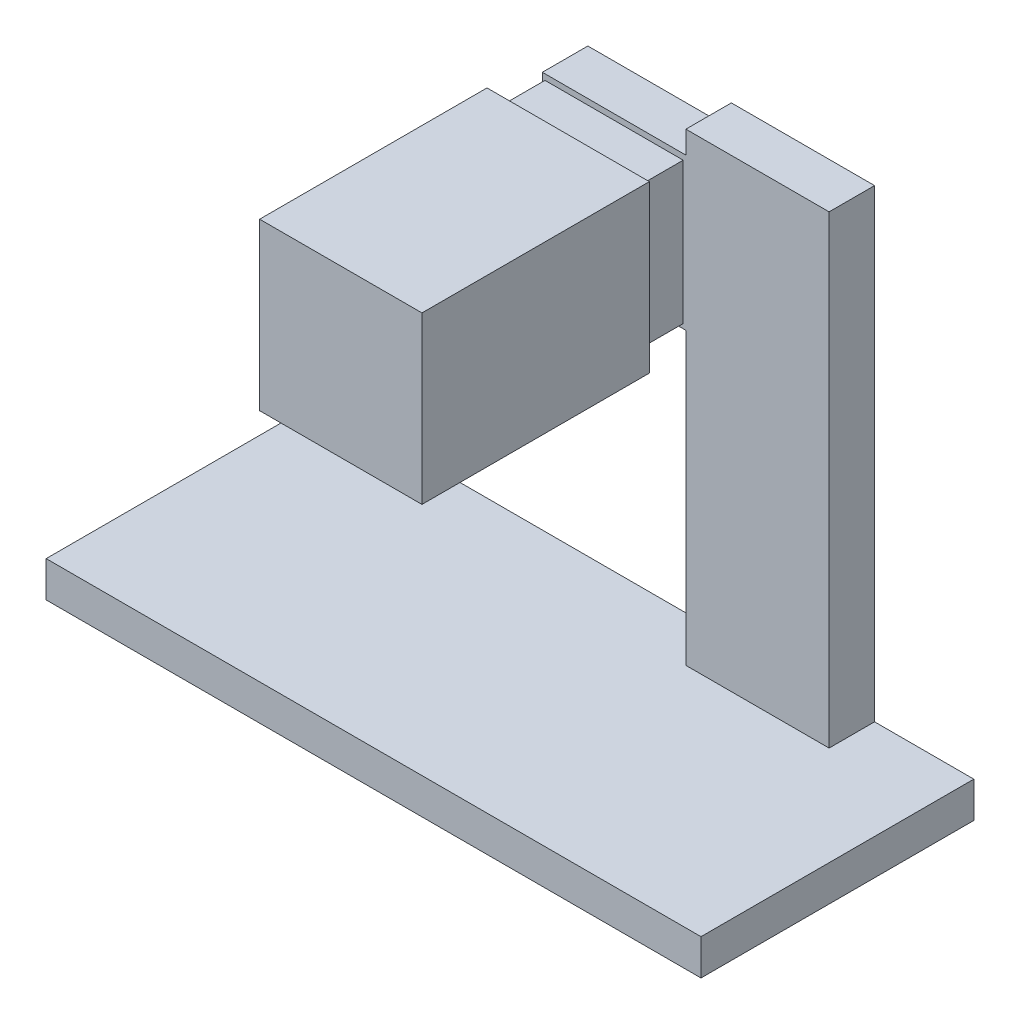
SolidWorks part; units mm, degrees
ref_plane "Front Plane" through (0, 0, 0) normal (0, 0, 1) x (1, 0, 0)
ref_plane "Top Plane" through (0, 0, 0) normal (0, 1, 0) x (1, 0, 0)
ref_plane "Right Plane" through (0, 0, 0) normal (1, 0, 0) x (0, 0, -1)
sketch "Sketch1" plane through (0, 0, 0) normal (0, 1, 0) x (1, 0, 0)
  line L1 (0, 0) -> (182.88, 0)
  line L2 (0, 0) -> (0, 76.2)
  line L3 (0, 76.2) -> (182.88, 76.2)
  line L4 (182.88, 0) -> (182.88, 76.2)
  dimension "D1" = 182.88
  dimension "D2" = 76.2
extrude "Boss-Extrude1" add sketch "Sketch1" along normal blind 10
sketch "Sketch2" plane through (0, 10, 0) normal (0, 1, 0) x (1, 0, 0)
  line L0 (182.88, 76.2) -> (0, 76.2) construction
  line L1 (115.1595, 76.2) -> (155.1595, 76.2)
  line L2 (115.1595, 76.2) -> (115.1595, 63.5)
  line L3 (115.1595, 63.5) -> (155.1595, 63.5)
  line L4 (155.1595, 76.2) -> (155.1595, 63.5)
  dimension "D1" = 40
  dimension "D2" = 12.7
extrude "Boss-Extrude2" add sketch "Sketch2" along normal blind 129.7
sketch "Sketch3" plane through (0, 0, -76.2) normal (0, 0, -1) x (-1, 0, 0)
  line L0 (-155.1595, 139.7) -> (-155.1595, 10) construction
  line L1 (-155.1595, 133.4194) -> (-75.0795, 133.4194)
  line L2 (-155.1595, 133.4194) -> (-155.1595, 91.0398)
  line L3 (-155.1595, 91.0398) -> (-75.0795, 91.0398)
  line L4 (-75.0795, 133.4194) -> (-75.0795, 91.0398)
extrude "Boss-Extrude3" add sketch "Sketch3" against normal up to surface (12.7 mm away) up to face at (135.1595, 74.85, -63.5)
sketch "Sketch4" plane through (0, 0, -63.5) normal (0, 0, 1) x (1, 0, 0)
  line L1 (75.8099, 131.8197) -> (114.4104, 131.8197)
  line L2 (75.8099, 131.8197) -> (75.8099, 92.3028)
  line L3 (75.8099, 92.3028) -> (114.4104, 92.3028)
  line L4 (114.4104, 131.8197) -> (114.4104, 92.3028)
extrude "Boss-Extrude4" add sketch "Sketch4" along normal blind 12.7
sketch "Sketch6" plane through (0, 0, -50.8) normal (0, 0, 1) x (1, 0, 0)
  line L1 (72.3199, 134.6021) -> (117.6562, 134.6021)
  line L2 (72.3199, 134.6021) -> (72.3199, 88.2802)
  line L3 (72.3199, 88.2802) -> (117.6562, 88.2802)
  line L4 (117.6562, 134.6021) -> (117.6562, 88.2802)
extrude "Boss-Extrude5" add sketch "Sketch6" along normal blind 63.5
sketch "Sketch7" plane through (0, 0, 12.7) normal (0, 0, 1) x (1, 0, 0)
  circle A0 centre (94.9881, 111.4412) radius 6.35
  dimension "D1" = 12.7
extrude "Boss-Extrude6" add sketch "Sketch7" against normal blind 99.06
